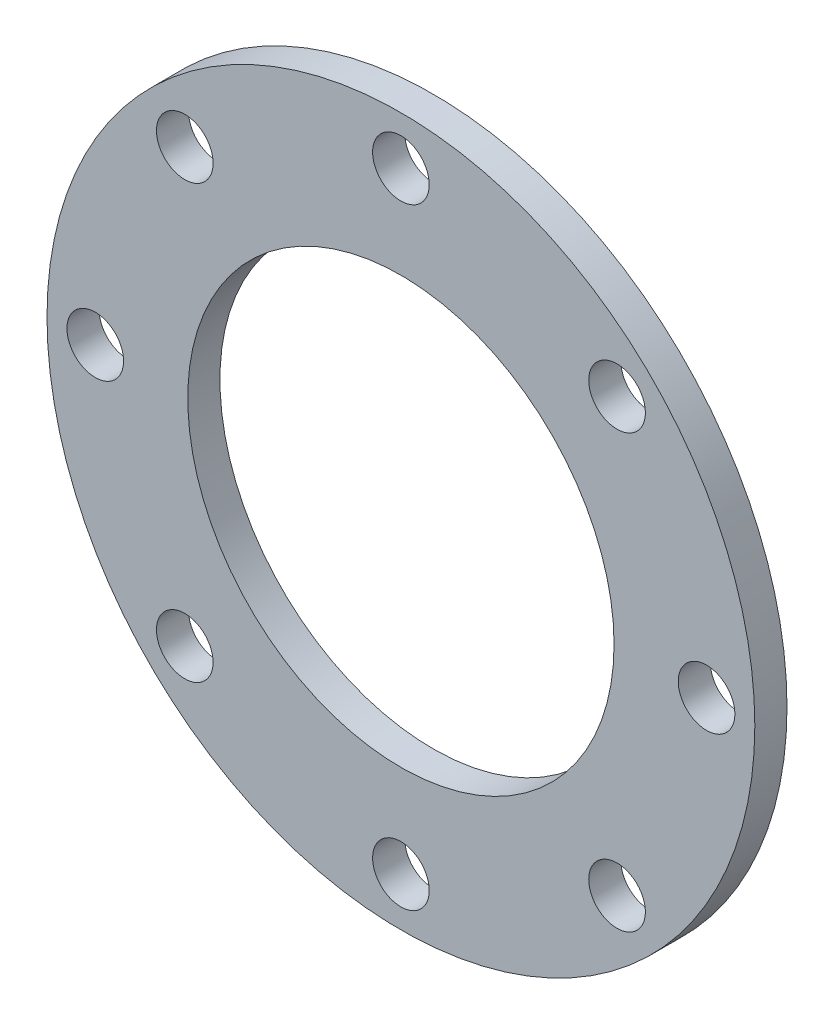
SolidWorks part; units mm, degrees
material "Ductile Iron"
ref_plane "Front Plane" through (0, 0, 0) normal (0, 0, 1) x (1, 0, 0)
ref_plane "Top Plane" through (0, 0, 0) normal (0, 1, 0) x (1, 0, 0)
ref_plane "Right Plane" through (0, 0, 0) normal (1, 0, 0) x (0, 0, -1)
sketch "Sketch1" plane through (0, 0, 0) normal (0, 0, 1) x (1, 0, 0)
  circle A0 centre (0, 0) radius 139.7
  circle A1 centre (0, 0) radius 120.65 construction
  circle A2 centre (0, 0) radius 84.1375
  circle A3 centre (0, 120.65) radius 11.176 construction
  circle A4 centre (85.3124, 85.3124) radius 11.176 construction
  circle A5 centre (120.65, 0) radius 11.176 construction
  circle A6 centre (85.3124, -85.3124) radius 11.176 construction
  circle A7 centre (0, -120.65) radius 11.176 construction
  circle A8 centre (-85.3124, -85.3124) radius 11.176 construction
  circle A9 centre (-120.65, 0) radius 11.176 construction
  circle A10 centre (-85.3124, 85.3124) radius 11.176 construction
  point P23 (0, 0)
  dimension "D1" = 279.4
  dimension "D2" = 241.3
  dimension "D3" = 168.275
  dimension "D4" = 22.352
  dimension "D5" = 8
extrude "Boss-Extrude1" add sketch "Sketch1" along normal blind 12.7
hole_wizard "7/8 (0.88) Diameter Hole1" positions "3DSketch1" profile "Sketch2" hole size "7/8" standard "ANSI Inch" end condition through all
sketch3d "3DSketch1"
  point P0 (120.65, 0, 0)
  point P3 (120.65, 0, 12.7)
sketch "Sketch2" plane through (120.65, 0, 12.7) normal (1, 0, 0) x (0, -1, 0)
  line L0 (0, 0) -> (0, 12.7)
  line L1 (0, 12.7) -> (11.176, 12.7)
  line L2 (11.176, 12.7) -> (11.176, 0)
  line L5 (11.176, 0) -> (0, 0)
  line L11 (0, -6.35) -> (0, 107.95) construction
  dimension "Thru Hole Dia." = 22.352
  dimension "Thru Hole Depth" = 12.7
pattern_circular "CirPattern1" count 8 over 360 about axis through (0, 0, 0) along (0, 0, 1) of "7/8 (0.88) Diameter Hole1"
equation "\"ID\"= 6.62500000in"
equation "\"BC\"= 9.5in"
equation "\"OD\"= 11in"
equation "\"HD\"= 0.88in"
equation "\"T\"= 0.5in"
equation "\"D1@Sketch1\"=\"OD\""
equation "\"D2@Sketch1\"=\"BC\""
equation "\"D3@Sketch1\"=\"ID\""
equation "\"D4@Sketch1\"=\"HD\""
equation "\"D1@Boss-Extrude1\"=\"T\""
